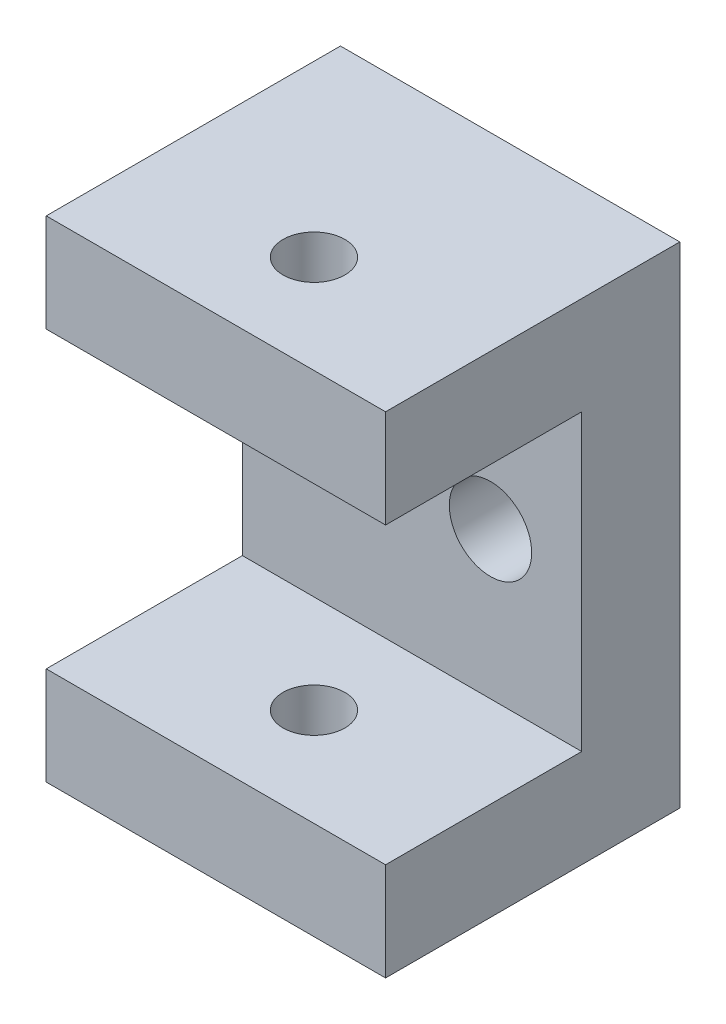
SolidWorks part; units mm, degrees
ref_plane "Спереди" through (0, 0, 0) normal (0, 0, 1) x (1, 0, 0)
ref_plane "Сверху" through (0, 0, 0) normal (0, 1, 0) x (1, 0, 0)
ref_plane "Справа" through (0, 0, 0) normal (1, 0, 0) x (0, 0, -1)
sketch "Sketch1" plane through (0, 0, 0) normal (0, 0, 1) x (1, 0, 0)
  line L0 (8, 0) -> (-8, 0) construction
  line L1 (17.3, -25) -> (-17.3, -25)
  line L2 (17.3, -25) -> (17.3, 25)
  line L3 (17.3, 25) -> (-17.3, 25)
  line L4 (-17.3, -25) -> (-17.3, 25)
  line L5 (17.3, -25) -> (-17.3, 25) construction
  line L6 (17.3, 25) -> (-17.3, -25) construction
  circle A0 centre (-8, 0) radius 4.2
  circle A1 centre (8, 0) radius 4.2
  point P0 (0, 0)
  point P9 (0, 0)
  dimension "D4" = 8.4
  dimension "D1" = 50
  dimension "D2" = 34.6
  dimension "D3" = 16
extrude "Boss-Extrude1" add sketch "Sketch1" along normal blind 30
sketch "Sketch2" plane through (-17.3, 0, 0) normal (-1, 0, 0) x (0, 0, 1)
  line L0 (20, -25) -> (20, 25) construction
  line L1 (30, -25) -> (0, -25) construction
  line L2 (30, 25) -> (0, 25) construction
  line L3 (30, 25) -> (30, -25) construction
  line L4 (10, 15) -> (30, 15)
  line L5 (10, 15) -> (10, -15)
  line L6 (10, -15) -> (30, -15)
  line L7 (30, 15) -> (30, -15)
  line L8 (10, 15) -> (30, -15) construction
  line L9 (10, -15) -> (30, 15) construction
  line L10 (0, 25) -> (0, -25) construction
  point P6 (20, 0)
  dimension "D1" = 10
  dimension "D2" = 10
extrude "Cut-Extrude1" cut sketch "Sketch2" against normal through all
sketch "Sketch3" plane through (0, 25, 0) normal (0, 1, 0) x (1, 0, 0)
  line L0 (0, -30) -> (0, 0) construction
  line L1 (17.3, -30) -> (-17.3, -30) construction
  line L2 (17.3, 0) -> (-17.3, 0) construction
  circle A0 centre (0, -20) radius 3.15
  dimension "D1" = 6.3
  dimension "D2" = 10
extrude "Cut-Extrude2" cut sketch "Sketch3" against normal through all
